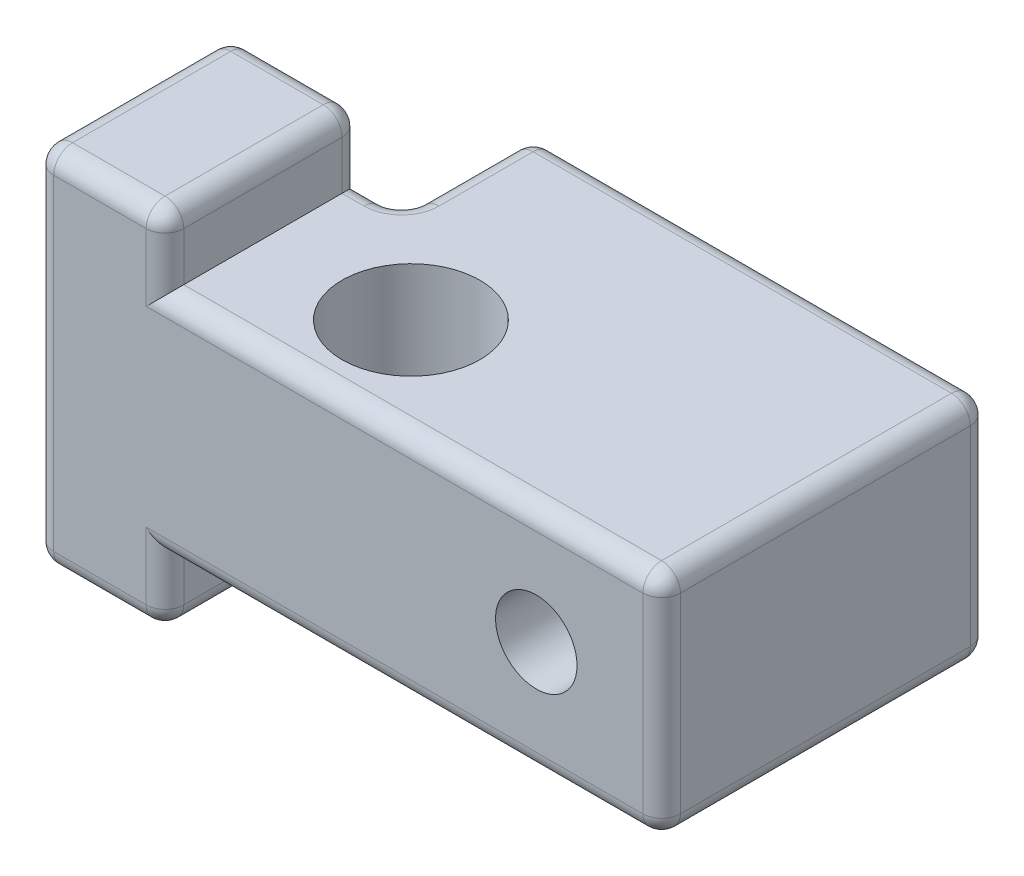
SolidWorks part; units mm, degrees
ref_plane "Front" through (0, 0, 0) normal (0, 0, 1) x (1, 0, 0)
ref_plane "Top" through (0, 0, 0) normal (0, 1, 0) x (1, 0, 0)
ref_plane "Right" through (0, 0, 0) normal (1, 0, 0) x (0, 0, -1)
sketch "Sketch1" plane through (0, 0, 0) normal (0, 1, 0) x (1, 0, 0)
  line L0 (-11.1125, 3.81) -> (-4.191, 3.81)
  line L1 (-4.191, 3.81) -> (-4.191, 9.144)
  line L3 (14.2875, 9.144) -> (14.2875, -6.6675)
  line L4 (14.2875, -6.6675) -> (-11.1125, -6.6675)
  line L5 (-11.1125, -6.6675) -> (-11.1125, 3.81)
  line L7 (0, 9.144) -> (0, 0) construction
  line L8 (-11.1125, 0) -> (0, 0) construction
  line L9 (14.2875, 9.144) -> (-4.191, 9.144)
  circle A0 centre (0, 0) radius 2.794
  dimension "D1" = 5.588
  dimension "D2" = 10.4775
  dimension "D3" = 11.1125
  dimension "D4" = 9.144
  dimension "D5" = 5.334
  dimension "D6" = 25.4
  dimension "D7" = 6.9215
extrude "Boss-Extrude1" add sketch "Sketch1" along normal mid plane 9.271
sketch "Sketch3" plane through (0, 0, 0) normal (0, 1, 0) x (1, 0, 0)
  line L0 (-11.1125, -6.6675) -> (-11.1125, 3.81) construction
  line L8 (-5.842, -6.6675) -> (-11.1125, -6.6675)
  line L9 (-5.842, -6.6675) -> (-5.842, 3.81)
  line L10 (-5.842, 3.81) -> (-11.1125, 3.81)
  line L11 (-11.1125, -6.6675) -> (-11.1125, 3.81)
  line L13 (14.2875, -6.6675) -> (-11.1125, -6.6675) construction
  line L14 (-11.1125, 3.81) -> (-4.191, 3.81) construction
  line L15 (0, 9.144) -> (0, 0) construction
  dimension "D2" = 5.842
extrude "Boss-Extrude3" add sketch "Sketch3" along normal mid plane 14.732
sketch "Sketch5" plane through (0, 0, 6.6675) normal (0, 0, 1) x (1, 0, 0)
  line L0 (14.2875, 0) -> (9.2075, 0) construction
  line L1 (14.2875, 4.6355) -> (14.2875, -4.6355) construction
  circle A0 centre (9.2075, 0) radius 1.651
  dimension "D2" = 3.302
  dimension "D1" = 5.08
extrude "Cut-Extrude2" cut sketch "Sketch5" against normal up to surface (15.8115 mm away) up to face at (5.0483, 0, -9.144)
sketch "Sketch6" plane through (0, 4.6355, 0) normal (0, 1, 0) x (1, 0, 0)
  line L0 (-11.1125, 3.81) -> (-11.1125, -6.6675) construction
  line L1 (-11.1125, -4.1275) -> (14.2875, -4.1275)
  line L2 (-11.1125, -4.1275) -> (-11.1125, -6.6675)
  line L3 (-11.1125, -6.6675) -> (14.2875, -6.6675)
  line L4 (14.2875, -4.1275) -> (14.2875, -6.6675)
  line L5 (14.2875, -6.6675) -> (14.2875, 9.144) construction
  dimension "D1" = 2.54
extrude "Cut-Extrude3" cut sketch "Sketch6" along normal up to surface and the other way up to surface up to face at (-8.4772, 7.366, 1.4288) other way up to face at (-8.4772, -7.366, 1.4288)
fillet "Fillet1" radius 0.762 28 edges at (-4.191, 0, -9.144) (-4.191, 4.6355, -6.477) (-4.191, -4.6355, -6.477) (-5.842, -6.0008, -3.81) (-5.0165, -4.6355, -3.81) (-4.191, 0, -3.81) (-5.0165, 4.6355, -3.81) (-5.842, 6.0008, -3.81) (-11.1125, 0, -3.81) (-8.4772, -7.366, -3.81) (-11.1125, -7.366, 0.1587) (-5.842, -7.366, 0.1587) (14.2875, 4.6355, -2.5083) (14.2875, 0, -9.144) (14.2875, -4.6355, -2.5083) (-11.1125, 7.366, 0.1587) (-8.4772, 7.366, -3.81) (-5.842, 7.366, 0.1587) (5.0483, -4.6355, -9.144) (5.0483, 4.6355, -9.144) (-8.4772, -7.366, 4.1275) (14.2875, 0, 4.1275) (-8.4772, 7.366, 4.1275) (-5.842, -6.0008, 4.1275) (4.2228, -4.6355, 4.1275) (-11.1125, 0, 4.1275) (4.2228, 4.6355, 4.1275) (-5.842, 6.0008, 4.1275)
